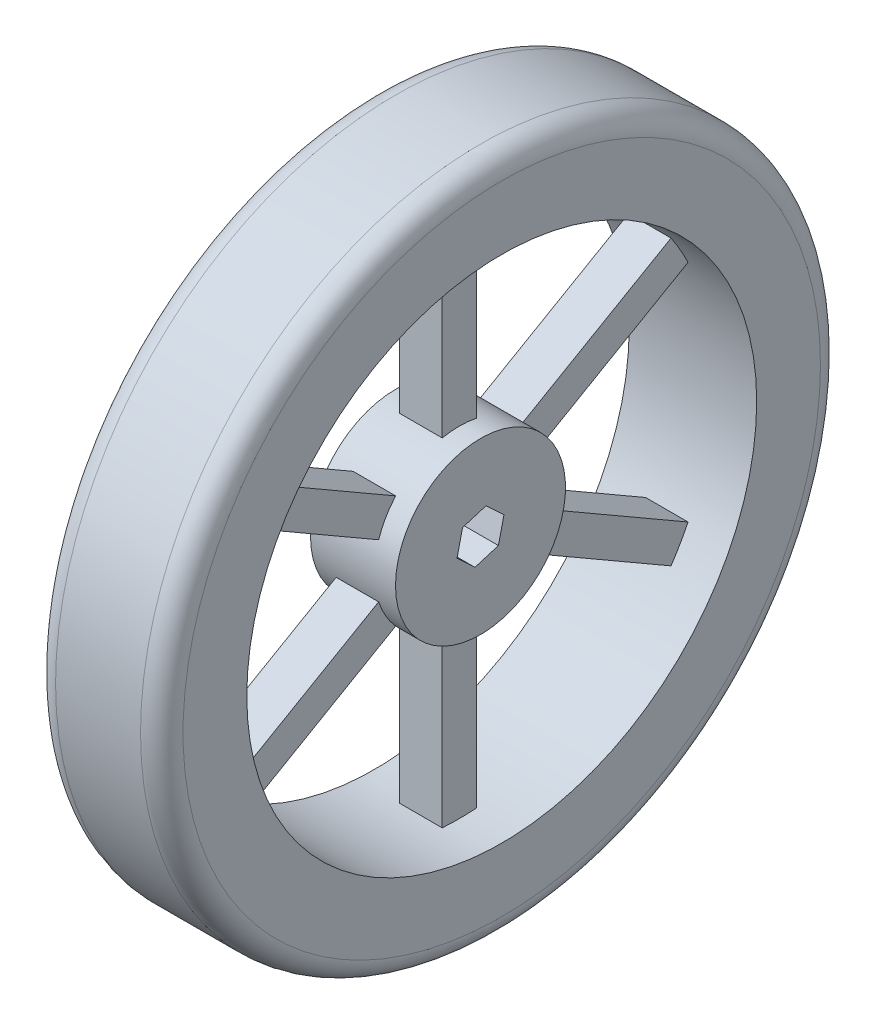
SolidWorks part; units mm, degrees
ref_plane "Front" through (0, 0, 0) normal (0, 0, 1) x (1, 0, 0)
ref_plane "Top" through (0, 0, 0) normal (0, 1, 0) x (1, 0, 0)
ref_plane "Right" through (0, 0, 0) normal (1, 0, 0) x (0, 0, -1)
sketch "Sketch1" plane through (0, 0, 0) normal (1, 0, 0) x (0, 0, -1)
  circle A0 centre (0, 0) radius 101.6
  circle A1 centre (0, 0) radius 76.2
  dimension "D1" = 203.2
  dimension "D2" = 25.4
extrude "Boss-Extrude1" add sketch "Sketch1" along normal blind 38.1
fillet "Fillet1" radius 6.35 2 edges at (0, 0, -101.6) (38.1, 0, -101.6)
ref_plane "Plane1" through (19.05, 0, 0) normal (-1, 0, 0) x (0, 0, 1)
sketch "Sketch2" plane through (19.05, 0, 0) normal (-1, 0, 0) x (0, 0, 1)
  line L1 (-5.3568, -5.0068) -> (1.6577, -7.1425)
  line L2 (1.6577, -7.1425) -> (7.0144, -2.1357)
  line L3 (7.0144, -2.1357) -> (5.3568, 5.0068)
  line L4 (5.3568, 5.0068) -> (-1.6577, 7.1425)
  line L5 (-1.6577, 7.1425) -> (-7.0144, 2.1357)
  line L6 (-7.0144, 2.1357) -> (-5.3568, -5.0068)
  circle A0 centre (0, 0) radius 25.4
  circle A1 centre (0, 0) radius 6.35 construction
extrude "Boss-Extrude2" add sketch "Sketch2" along normal blind 12.7 and the other way blind 12.7 separate body
sketch "Sketch3" plane through (19.05, 0, 0) normal (-1, 0, 0) x (0, 0, 1)
  line L0 (0, 0) -> (0, 87.8109) construction
  line L1 (6.9331, 9.8786) -> (12.0217, 1.0649)
  line L2 (-5.0886, 10.9435) -> (5.0886, 10.9435)
  line L3 (-5.0886, 10.9435) -> (-5.0886, 76.8673)
  line L4 (-5.0886, 76.8673) -> (5.0886, 76.8673)
  line L5 (5.0886, 10.9435) -> (5.0886, 76.8673)
  line L6 (-5.0886, 10.9435) -> (5.0886, 76.8673) construction
  line L7 (-5.0886, 76.8673) -> (5.0886, 10.9435) construction
  line L8 (6.9331, 9.8786) -> (64.0248, 42.8405)
  line L9 (64.0248, 42.8405) -> (69.1134, 34.0268)
  line L10 (12.0217, 1.0649) -> (69.1134, 34.0268)
  line L11 (6.9331, 9.8786) -> (69.1134, 34.0268) construction
  line L12 (64.0248, 42.8405) -> (12.0217, 1.0649) construction
  line L13 (12.0217, -1.0649) -> (6.9331, -9.8786)
  line L14 (12.0217, -1.0649) -> (69.1134, -34.0268)
  line L15 (69.1134, -34.0268) -> (64.0248, -42.8405)
  line L16 (6.9331, -9.8786) -> (64.0248, -42.8405)
  line L17 (12.0217, -1.0649) -> (64.0248, -42.8405) construction
  line L18 (69.1134, -34.0268) -> (6.9331, -9.8786) construction
  line L19 (5.0886, -10.9435) -> (-5.0886, -10.9435)
  line L20 (5.0886, -10.9435) -> (5.0886, -76.8673)
  line L21 (5.0886, -76.8673) -> (-5.0886, -76.8673)
  line L22 (-5.0886, -10.9435) -> (-5.0886, -76.8673)
  line L23 (5.0886, -10.9435) -> (-5.0886, -76.8673) construction
  line L24 (5.0886, -76.8673) -> (-5.0886, -10.9435) construction
  line L25 (-6.9331, -9.8786) -> (-12.0217, -1.0649)
  line L26 (-6.9331, -9.8786) -> (-64.0248, -42.8405)
  line L27 (-64.0248, -42.8405) -> (-69.1134, -34.0268)
  line L28 (-12.0217, -1.0649) -> (-69.1134, -34.0268)
  line L29 (-6.9331, -9.8786) -> (-69.1134, -34.0268) construction
  line L30 (-64.0248, -42.8405) -> (-12.0217, -1.0649) construction
  line L31 (-12.0217, 1.0649) -> (-6.9331, 9.8786)
  line L32 (-12.0217, 1.0649) -> (-69.1134, 34.0268)
  line L33 (-69.1134, 34.0268) -> (-64.0248, 42.8405)
  line L34 (-6.9331, 9.8786) -> (-64.0248, 42.8405)
  line L35 (-12.0217, 1.0649) -> (-64.0248, 42.8405) construction
  line L36 (-69.1134, 34.0268) -> (-6.9331, 9.8786) construction
  point P3 (0, 43.9054)
  point P8 (0, 0)
  point P9 (0, 0)
  point P10 (38.0232, 21.9527)
  point P15 (38.0232, -21.9527)
  point P20 (0, -43.9054)
  point P25 (-38.0232, -21.9527)
  point P30 (-38.0232, 21.9527)
  point P35 (0, 0)
  point P36 (4.5652, 11.2568)
  point P37 (0, 0)
  point P38 (8.1626, 73.4761)
  point P39 (5.0886, 76.8673)
  dimension "D1" = 6
extrude "Boss-Extrude3" add sketch "Sketch3" along normal blind 6.35 and the other way blind 6.35
